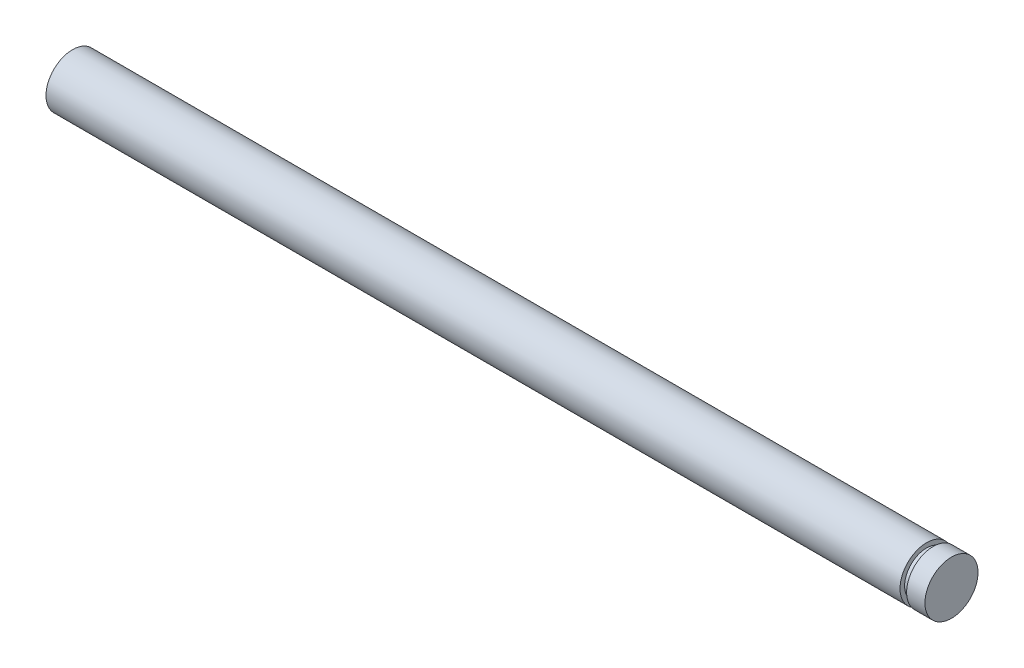
SolidWorks part; units mm, degrees
ref_plane "Front Plane" through (0, 0, 0) normal (0, 0, 1) x (1, 0, 0)
ref_plane "Top Plane" through (0, 0, 0) normal (0, 1, 0) x (1, 0, 0)
ref_plane "Right Plane" through (0, 0, 0) normal (1, 0, 0) x (0, 0, -1)
sketch "Sketch1" plane through (0, 0, 0) normal (0, 0, 1) x (1, 0, 0)
  line L0 (0, 0) -> (0, 0.725)
  line L1 (0, 0.725) -> (23.32, 0.725)
  line L2 (23.32, 0.725) -> (23.32, 0.6)
  line L3 (23.32, 0.6) -> (23.5, 0.6)
  line L4 (23.5, 0.6) -> (23.5, 0.725)
  line L5 (23.5, 0.725) -> (24, 0.725)
  line L6 (24, 0.725) -> (24, 0)
  line L7 (24, 0) -> (0, 0)
  dimension "D1" = 0.725
  dimension "D2" = 24
  dimension "D3" = 0.6
  dimension "D4" = 0.18
  dimension "D5" = 0.5
revolve "Revolve1" add sketch "Sketch1" angle 360 about L7
